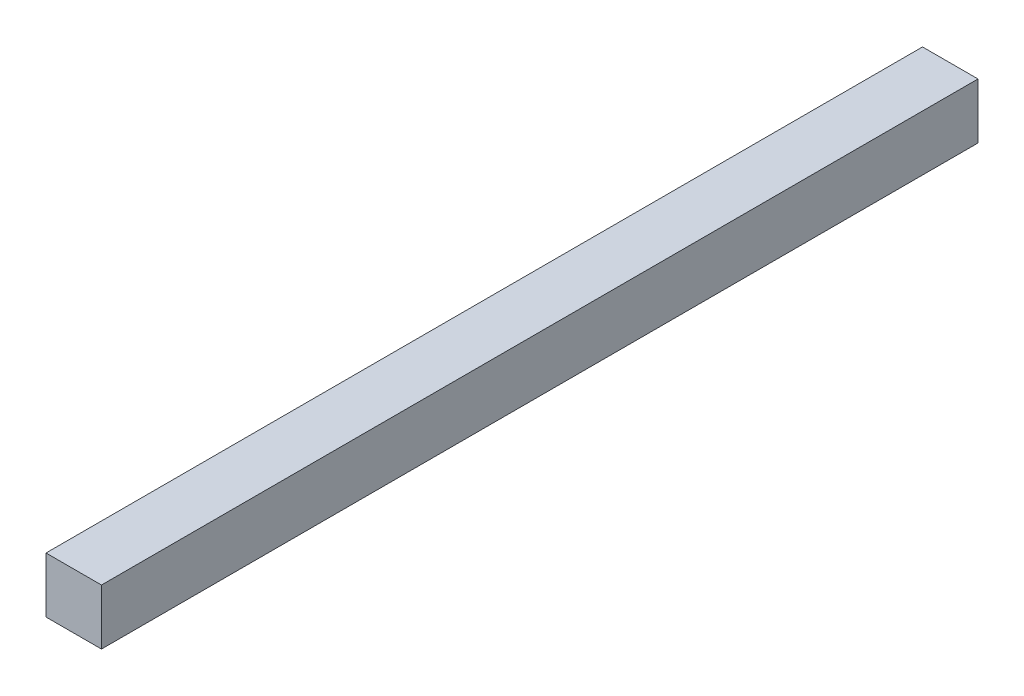
SolidWorks part; units mm, degrees
ref_plane "Alzado" through (0, 0, 0) normal (0, 0, 1) x (1, 0, 0)
ref_plane "Planta" through (0, 0, 0) normal (0, 1, 0) x (1, 0, 0)
ref_plane "Vista lateral" through (0, 0, 0) normal (1, 0, 0) x (0, 0, -1)
sketch "Croquis1" plane through (0, 0, 0) normal (0, 1, 0) x (1, 0, 0)
  line L1 (0, 0) -> (10, 0)
  line L2 (0, 0) -> (0, 158)
  line L3 (0, 158) -> (10, 158)
  line L4 (10, 0) -> (10, 158)
  dimension "D1" = 10
  dimension "D2" = 158
extrude "Saliente-Extruir1" add sketch "Croquis1" along normal blind 10
